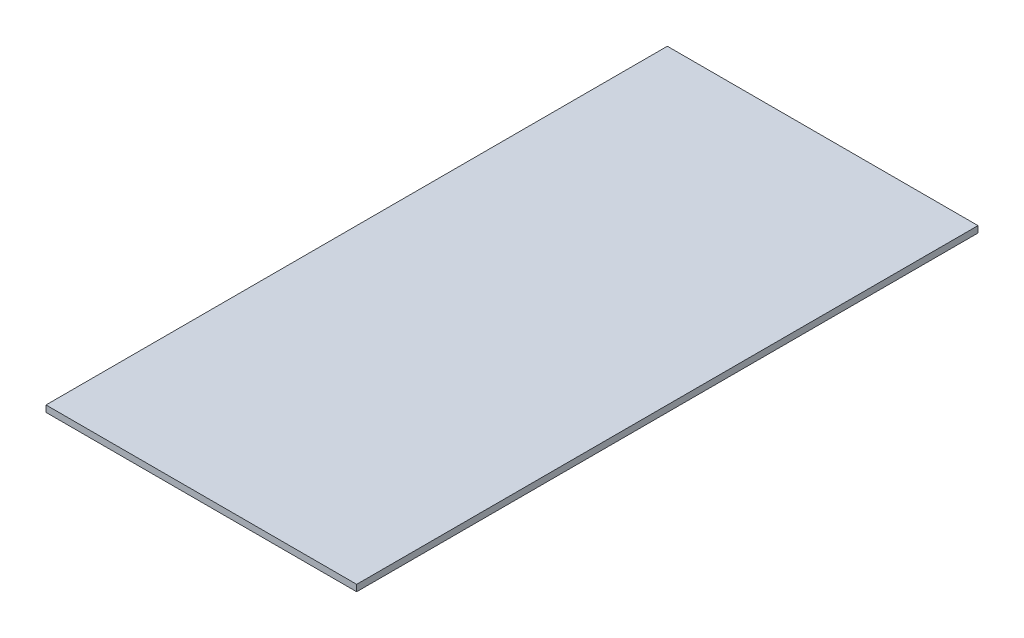
SolidWorks part; units mm, degrees
ref_plane "Front Plane" through (0, 0, 0) normal (0, 0, 1) x (1, 0, 0)
ref_plane "Top Plane" through (0, 0, 0) normal (0, 1, 0) x (1, 0, 0)
ref_plane "Right Plane" through (0, 0, 0) normal (1, 0, 0) x (0, 0, -1)
sketch "Sketch1" plane through (0, 0, 0) normal (0, 1, 0) x (1, 0, 0)
  line L1 (-609.6, 1219.2) -> (609.6, 1219.2)
  line L2 (-609.6, 1219.2) -> (-609.6, -1219.2)
  line L3 (-609.6, -1219.2) -> (609.6, -1219.2)
  line L4 (609.6, 1219.2) -> (609.6, -1219.2)
  line L5 (-609.6, 1219.2) -> (609.6, -1219.2) construction
  line L6 (-609.6, -1219.2) -> (609.6, 1219.2) construction
  point P0 (0, 0)
  dimension "D1" = 1219.2
  dimension "D2" = 2438.4
extrude "Boss-Extrude1" add sketch "Sketch1" against normal mid plane 25.4
